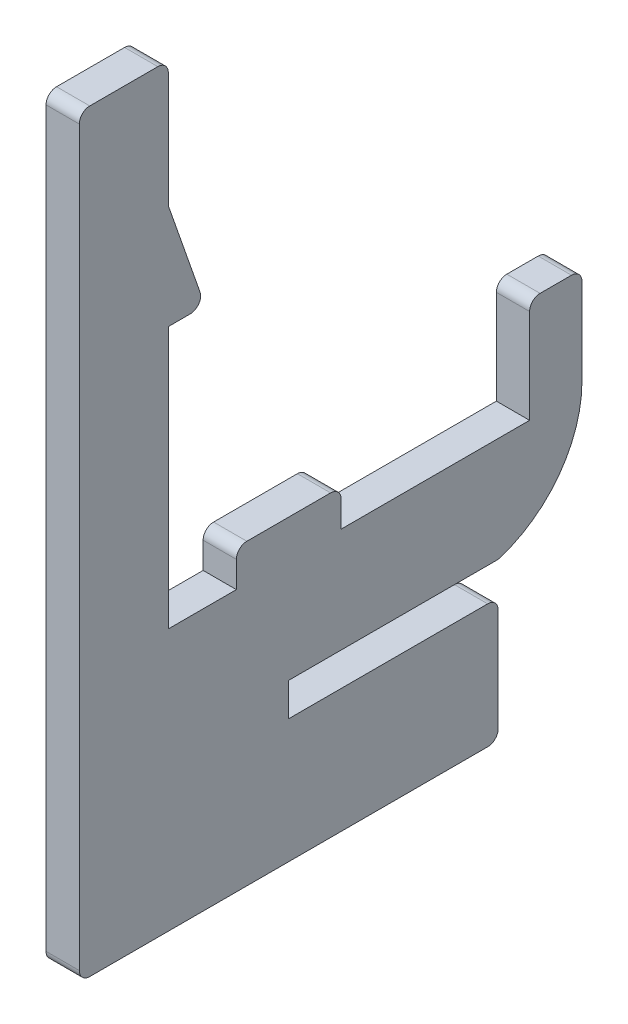
SolidWorks part; units mm, degrees
ref_plane "Front Plane" through (0, 0, 0) normal (0, 0, 1) x (1, 0, 0)
ref_plane "Top Plane" through (0, 0, 0) normal (0, 1, 0) x (1, 0, 0)
ref_plane "Right Plane" through (0, 0, 0) normal (1, 0, 0) x (0, 0, -1)
sketch "Sketch1" plane through (0, 0, 0) normal (1, 0, 0) x (0, 0, -1)
  line L0 (0, 0) -> (0, 25)
  line L1 (0, 0) -> (6.5, 0)
  line L2 (0, 25) -> (3.5, 25)
  line L3 (3.5, 25) -> (0, 35)
  line L4 (0, 35) -> (0, 47)
  line L5 (6.5, 0) -> (6.5, 3.5)
  line L6 (6.5, 3.5) -> (16.5, 3.5)
  line L7 (16.5, 3.5) -> (16.5, 0)
  line L8 (16.5, 0) -> (34.5, 0)
  line L9 (34.5, 0) -> (34.5, 10)
  line L10 (31.5, -10) -> (-8.5, -10)
  line L11 (34.5, 10) -> (39.5, 10)
  line L12 (39.5, 10) -> (39.5, 0.7217)
  line L13 (0, 47) -> (-8.5, 47)
  line L14 (-8.5, 47) -> (-8.5, -10)
  line L15 (-8.5, -10) -> (-8.5, -25)
  line L16 (-8.5, -25) -> (31.5, -25)
  line L17 (31.5, -25) -> (31.5, -13.175)
  line L18 (31.5, -13.175) -> (11.5, -13.175)
  line L19 (11.5, -13.175) -> (11.5, -10)
  arc A0 (39.5, 0.7217) -> (31.5, -10) centre (28.3153, 0.7217) cw
  point P24 (11.5, -10)
  point P25 (11.5, 3.5)
  dimension "D12" = 25
  dimension "D13" = 15
  dimension "D14" = 3.175
  dimension "D15" = 5
  dimension "D2" = 6.5
  dimension "D3" = 3.5
  dimension "D4" = 10
  dimension "D5" = 12
  dimension "D6" = 10
  dimension "D7" = 3.5
  dimension "D8" = 18
  dimension "D9" = 10
  dimension "D10" = 40
  dimension "D11" = 10
extrude "Boss-Extrude1" add sketch "Sketch1" along normal blind 3.175
fillet "Fillet1" radius 1 11 edges at (1.5875, -25, 8.5) (1.5875, -25, -31.5) (1.5875, -13.175, -31.5) (1.5875, 3.5, -6.5) (1.5875, 3.5, -16.5) (1.5875, 47, 8.5) (1.5875, 47, 0) (1.5875, 10, -34.5) (1.5875, 25, -3.5) (1.5875, -10, -31.5) (1.5875, 10, -39.5)
